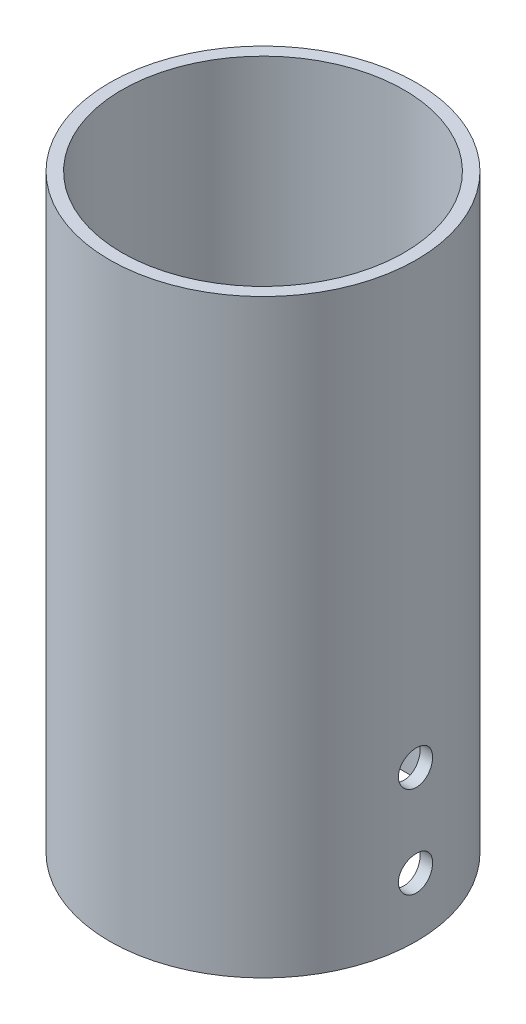
SolidWorks part; units mm, degrees
ref_plane "Front Plane" through (0, 0, 0) normal (0, 0, 1) x (1, 0, 0)
ref_plane "Top Plane" through (0, 0, 0) normal (0, 1, 0) x (1, 0, 0)
ref_plane "Right Plane" through (0, 0, 0) normal (1, 0, 0) x (0, 0, -1)
sketch "Sketch1" plane through (0, 0, 0) normal (0, 1, 0) x (1, 0, 0)
  circle A0 centre (0, 0) radius 26
  circle A1 centre (0, 0) radius 23.9
  dimension "D1" = 52
  dimension "D2" = 47.8
extrude "Boss-Extrude1" add sketch "Sketch1" along normal blind 100
sketch "Sketch2" plane through (0, 0, 0) normal (1, 0, 0) x (0, 0, -1)
  line L0 (0, 0) -> (0, 10)
  line L1 (0, 10) -> (0, 25.5)
  circle A0 centre (0, 10) radius 2.9
  circle A1 centre (0, 25.5) radius 2.9
  dimension "D1" = 5.8
  dimension "D2" = 5.8
  dimension "D3" = 10
  dimension "D4" = 15.5
extrude "Cut-Extrude1" cut sketch "Sketch2" against normal through all both and the other way through all
equation "\"TubeOutsideDiameter\"= 52"
equation "\"D1@Sketch1\"=\"TubeOutsideDiameter\""
equation "\"TubeInnerDiameter\"= 47.8"
equation "\"ReleaseMechanisumHeight\"=100"
equation "\"WireDiameter\"=3.38983"
equation "\"servoHoleDiameter\" = 2.8"
equation "\"CordDiameter\"= 5"
equation "\"MountingBoldDiameter\"=2.8"
equation "\"TubeMountingBoltDiameter\" = 5"
equation "\"D2@Sketch1\"=\"TubeInnerDiameter\""
equation "\"CardTubeOutsideDiameter\"= 54.2"
equation "\"CardTubeInsideDiameter\"= 50.4"
equation "\"D1@Sketch2\"=\"TubeMountingBoltDiameter\"+0.8"
equation "\"D2@Sketch2\"=\"TubeMountingBoltDiameter\"+0.8"
